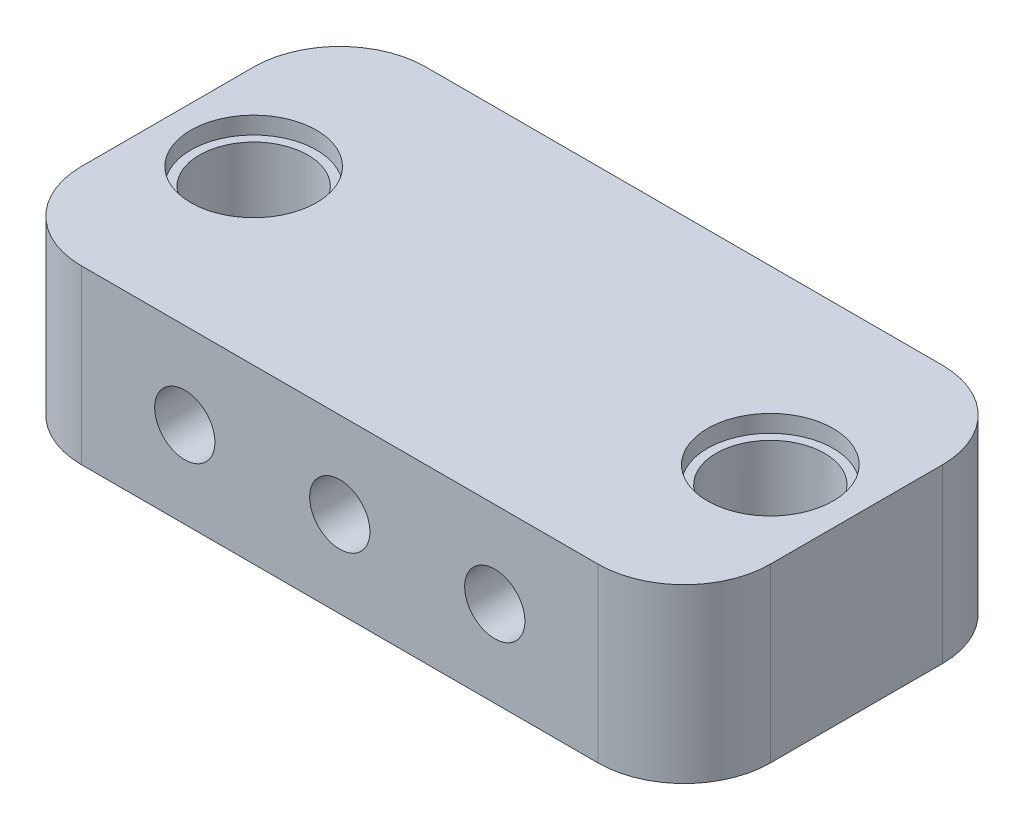
SolidWorks part; units mm, degrees
ref_plane "Plan de face" through (0, 0, 0) normal (0, 0, 1) x (1, 0, 0)
ref_plane "Plan de dessus" through (0, 0, 0) normal (0, 1, 0) x (1, 0, 0)
ref_plane "Plan de droite" through (0, 0, 0) normal (1, 0, 0) x (0, 0, -1)
sketch "Esquisse1" plane through (0, 0, 0) normal (0, 0, 1) x (1, 0, 0)
  line L1 (0, 0) -> (40, 0)
  line L2 (0, 0) -> (0, 10)
  line L3 (0, 10) -> (40, 10)
  line L4 (40, 0) -> (40, 10)
  dimension "D1" = 10
  dimension "D2" = 40
extrude "Boss.-Extru.1" add sketch "Esquisse1" along normal blind 20
sketch "Esquisse2" plane through (0, 0, 20) normal (0, 0, 1) x (1, 0, 0)
  line L0 (0, 5) -> (40, 5) construction
  line L1 (0, 10) -> (0, 0) construction
  line L2 (40, 0) -> (40, 10) construction
  line L3 (20, 10) -> (20, 0) construction
  line L4 (40, 10) -> (0, 10) construction
  line L5 (0, 0) -> (40, 0) construction
  circle A0 centre (20, 5) radius 1.75
  circle A1 centre (11, 5) radius 1.75
  circle A2 centre (29, 5) radius 1.75
  dimension "D1" = 3.5
  dimension "D2" = 18
extrude "Enlèv. mat.-Extru.1" cut sketch "Esquisse2" against normal through all both and the other way through all
sketch "Esquisse3" plane through (0, 10, 0) normal (0, 1, 0) x (1, 0, 0)
  line L0 (0, -10) -> (40, -10) construction
  line L1 (0, -20) -> (0, 0) construction
  line L2 (40, -20) -> (40, 0) construction
  line L3 (20, 0) -> (20, -10) construction
  line L4 (40, 0) -> (0, 0) construction
  circle A0 centre (5, -10) radius 3.15
  circle A1 centre (35, -10) radius 3.15
  dimension "D1" = 6.3
  dimension "D2" = 30
extrude "Enlèv. mat.-Extru.2" cut sketch "Esquisse3" against normal through all both and the other way through all
sketch "Esquisse4" plane through (0, 10, 0) normal (0, 1, 0) x (1, 0, 0)
  circle A0 centre (5, -10) radius 3.65
  circle A1 centre (35, -10) radius 3.65
  dimension "D1" = 7.3
extrude "Enlèv. mat.-Extru.3" cut sketch "Esquisse4" against normal blind 1
fillet "Congé1" radius 5 4 edges at (0, 5, 0) (0, 5, 20) (40, 5, 0) (40, 5, 20)
